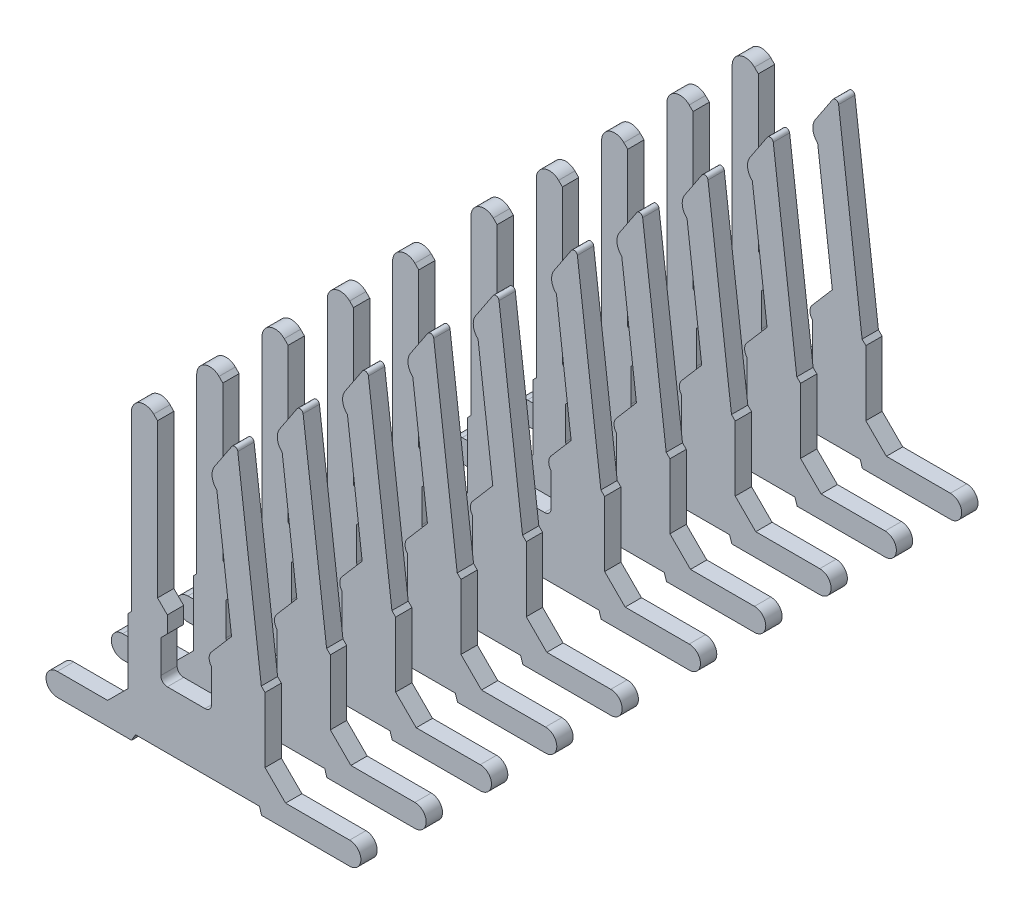
SolidWorks part; units mm, degrees
ref_plane "Płaszczyzna przednia" through (0, 0, 0) normal (0, 0, 1) x (1, 0, 0)
ref_plane "Płaszczyzna górna" through (0, 0, 0) normal (0, 1, 0) x (1, 0, 0)
ref_plane "Płaszczyzna prawa" through (0, 0, 0) normal (1, 0, 0) x (0, 0, -1)
sketch "Sketch1" plane through (0, 0, 0) normal (0, 0, 1) x (1, 0, 0)
  line L52 (1.1543, 1.456) -> (1.0969, 1.5134)
  line L53 (1.0969, 1.5134) -> (0.7371, 4.4438)
  line L54 (0.6458, 4.4654) -> (0.3804, 4.0662)
  line L55 (0.4165, 3.7723) -> (0.6414, 1.9409)
  line L56 (0.6414, 1.9409) -> (0.3345, 1.5836)
  line L57 (0.3345, 1.3881) -> (0.3345, 0.8832)
  line L58 (0.2345, 0.7832) -> (-0.3421, 0.7832)
  line L59 (-0.4421, 0.8832) -> (-0.4421, 1.3849)
  line L60 (-0.4421, 1.3849) -> (-0.3421, 1.4849)
  line L61 (-0.3421, 1.4849) -> (-0.3421, 1.7374)
  line L62 (-0.3421, 1.7374) -> (-0.4921, 1.8874)
  line L63 (-0.4921, 1.8874) -> (-0.4921, 4.2369)
  line L64 (-0.4921, 4.2369) -> (-0.5507, 4.2955)
  line L65 (-0.8921, 4.154) -> (-0.8921, 1.506)
  line L66 (-0.8921, 1.506) -> (-0.9421, 1.456)
  line L67 (-0.9421, 1.456) -> (-0.9421, 0.4604)
  line L68 (-0.9421, 0.4604) -> (-1.2566, 0.1459)
  line L69 (-1.2566, 0.1459) -> (-2.027, 0.1459)
  line L70 (-2.027, -0.2) -> (-0.8897, -0.2)
  line L71 (-0.8897, -0.2) -> (-0.8292, -0.0952)
  line L72 (-0.8292, -0.0952) -> (1.0681, -0.0952)
  line L73 (1.0681, -0.0952) -> (1.1019, -0.2)
  line L74 (1.1019, -0.2) -> (2.4489, -0.2)
  line L75 (2.4489, 0.1459) -> (1.4688, 0.1459)
  line L76 (1.4688, 0.1459) -> (1.1543, 0.4604)
  line L77 (1.1543, 0.4604) -> (1.1543, 1.456)
  arc A16 (0.7371, 4.4438) -> (0.6458, 4.4654) centre (0.6875, 4.4377) ccw
  arc A17 (0.3804, 4.0662) -> (0.4165, 3.7723) centre (0.5698, 3.9403) ccw
  arc A18 (0.3345, 1.5836) -> (0.3345, 1.3881) centre (0.4483, 1.4859) ccw
  arc A19 (0.2345, 0.7832) -> (0.3345, 0.8832) centre (0.2345, 0.8832) ccw
  arc A20 (-0.4421, 0.8832) -> (-0.3421, 0.7832) centre (-0.3421, 0.8832) ccw
  arc A21 (-0.5507, 4.2955) -> (-0.8921, 4.154) centre (-0.6921, 4.154) ccw
  arc A22 (-2.027, 0.1459) -> (-2.027, -0.2) centre (-2.027, -0.027) ccw
  arc A23 (2.4489, -0.2) -> (2.4489, 0.1459) centre (2.4489, -0.027) ccw
extrude "Boss-Extrude1" add sketch "Sketch1" along normal blind 0.25
pattern_linear "LPattern1" count 5 spacing 1 along (0, 0, -1) of bodies 101
pattern_linear "Szyk liniowy1" count 2 spacing 5.2 along (0, 0, -1) of bodies 101 102 103 104 105
